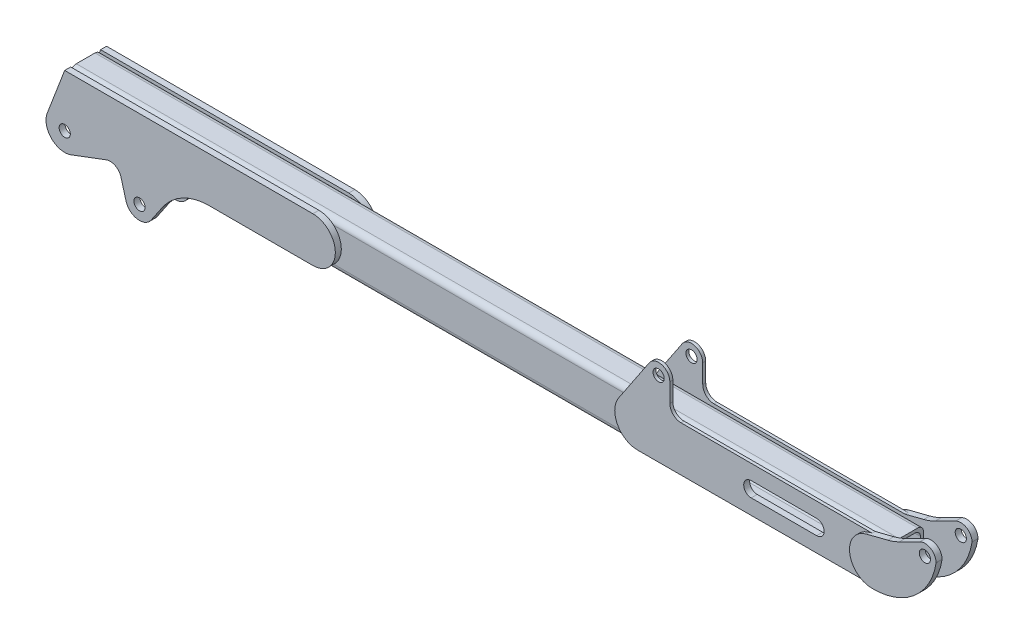
SolidWorks part; units mm, degrees
ref_plane "Front Plane" through (0, 0, 0) normal (0, 0, 1) x (1, 0, 0)
ref_plane "Top Plane" through (0, 0, 0) normal (0, 1, 0) x (1, 0, 0)
ref_plane "Right Plane" through (0, 0, 0) normal (1, 0, 0) x (0, 0, -1)
sketch "Sketch2" plane through (0, 0, 0) normal (1, 0, 0) x (0, 0, -1)
  line L0 (0, 0) -> (0, 180.6275) construction
  line L1 (-32, 132) -> (32, 132)
  line L2 (-40, 140) -> (40, 140)
  line L3 (-40, 140) -> (-40, 20)
  line L4 (-40, 20) -> (40, 20)
  line L5 (40, 140) -> (40, 20)
  line L6 (-40, 140) -> (40, 20) construction
  line L7 (-40, 20) -> (40, 140) construction
  line L8 (32, 132) -> (32, 28)
  line L9 (-32, 28) -> (32, 28)
  line L10 (-32, 132) -> (-32, 28)
  point P2 (0, 80)
  dimension "D1" = 80
  dimension "D2" = 120
  dimension "D4" = 80
  dimension "D3" = 8
extrude "Boss-Extrude1" add sketch "Sketch2" along normal blind 2200
fillet "Fillet4" radius 15 8 edges at (1100, 20, -40) (1100, 28, 32) (1100, 132, 32) (1100, 132, -32) (1100, 28, -32) (1100, 20, 40) (1100, 140, -40) (1100, 140, 40)
sketch "Sketch3" plane through (0, 0, 40) normal (0, 0, 1) x (1, 0, 0)
  line L0 (0, 80) -> (2300, 80) construction
  line L1 (0, 125) -> (0, 35) construction
  line L2 (-1929.687, -1730.7826) -> (-1056.3536, -1730.7826) construction
  line L3 (148.6635, -712.4908) -> (749.3302, -712.4908) construction
  line L4 (0, 0) -> (0, -650) construction
  line L5 (0, -650) -> (100, -650) construction
  dimension "D1" = 100
  dimension "D2" = 650
  dimension "D5" = 2300
sketch "Sketch4" plane through (0, 0, 40) normal (0, 0, 1) x (1, 0, 0)
  line L0 (0, 0) -> (200, 0.9743) construction
  line L1 (0, 80) -> (2300, 80) construction
  line L2 (663.6168, 140) -> (0, 140)
  line L3 (0, 140) -> (-46.7025, 17.8571)
  line L4 (17.6358, -46.7865) -> (141.757, 0)
  line L5 (141.757, 0) -> (163.854, -79.9858)
  line L6 (231.0313, -91.055) -> (306.383, 20)
  line L7 (2200, 20) -> (0, 20) construction
  line L8 (306.383, 20) -> (663.6168, 20)
  line L9 (200, 0.9743) -> (200, -70) construction
  circle A0 centre (0, 0) radius 15
  circle A1 centre (200, -70) radius 15
  arc A2 (663.6168, 20) -> (663.6168, 140) centre (663.6168, 80) ccw
  arc A3 (163.854, -79.9858) -> (231.0313, -91.055) centre (200, -70) ccw
  arc A4 (-46.7025, 17.8571) -> (17.6358, -46.7865) centre (0, 0) ccw
  dimension "D1" = 30
  dimension "D2" = 30
  dimension "D5" = 120
  dimension "D6" = 75
  dimension "D7" = 100
  dimension "D3" = 200
  dimension "D4" = 150
extrude "Boss-Extrude2" add sketch "Sketch4" along normal blind 16
fillet "Fillet1" radius 30 1 edges at (141.757, 0, 48)
fillet "Fillet2" radius 150 1 edges at (306.383, 20, 48)
ref_plane "Plane1" through (0, 0, 0) normal (0, 0, -1) x (-1, 0, 0)
mirror "Mirror1" about plane through (0, 0, 0) normal (0, 0, -1) of "Fillet2", "Fillet1", "Boss-Extrude2"
sketch "Sketch5" plane through (0, 0, 40) normal (0, 0, 1) x (1, 0, 0)
  line L1 (2300, 165) -> (2300, 80) construction
  line L2 (2286.519, 191.8004) -> (2216.8615, 156.7617)
  line L3 (2216.8615, 156.7617) -> (2143.6382, 138.1512)
  line L4 (0, 80) -> (2300, 80) construction
  circle A0 centre (2158.418, 80) radius 60
  circle A1 centre (2300, 165) radius 15
  circle A2 centre (2300, 165) radius 30
  arc A3 (2156.4729, 20.0315) -> (2330, 165) centre (2161.9788, 189.7811) ccw
  dimension "D1" = 30
  dimension "D2" = 60
  dimension "D3" = 85
  dimension "D4" = 120
extrude "Boss-Extrude3" add sketch "Sketch5" along normal blind 16 separate body
fillet "Fillet3" radius 150 1 edges at (2216.8615, 156.7617, 48)
sketch "Sketch9" plane through (0, 0, 40) normal (0, 0, 1) x (1, 0, 0)
  line L0 (0, 80) -> (2300, 80) construction
  line L1 (1610, 140) -> (2157.5508, 140)
  line L2 (0, 140) -> (2200, 140) construction
  line L3 (2157.5508, 140) -> (2157.5508, 20)
  line L4 (2157.5508, 20) -> (1524.007, 18.707)
  line L5 (2200, 20) -> (0, 20) construction
  line L6 (1473.0598, 114.0766) -> (1555.0638, 236.6789)
  line L7 (1610, 220) -> (1610, 140)
  arc A0 (1473.0598, 114.0766) -> (1524.007, 18.707) centre (1524.007, 80) ccw
  arc A1 (2156.4729, 20.0315) -> (2330, 165) centre (2161.9788, 189.7811) ccw construction
  circle A2 centre (1580, 220) radius 15
  arc A3 (1610, 220) -> (1555.0638, 236.6789) centre (1580, 220) ccw
  dimension "D1" = 30
  dimension "D2" = 60
  dimension "D3" = 1580
  dimension "D4" = 220
extrude "Boss-Extrude4" add sketch "Sketch9" along normal blind 8
fillet "Fillet5" radius 30 1 edges at (1610, 140, 44)
mirror "Mirror5" about plane through (0, 0, 0) normal (0, 0, -1) of "Fillet3", "Boss-Extrude3", "Fillet5", "Boss-Extrude4"
sketch "Sketch6" plane through (0, 0, 40) normal (0, 0, 1) x (1, 0, 0)
  line L0 (1827.553, 80) -> (2002.553, 80) construction
  line L1 (0, 80) -> (2300, 80) construction
  line L2 (1827.553, 100) -> (2002.553, 100)
  line L3 (1827.553, 60) -> (2002.553, 60)
  arc A0 (1827.553, 100) -> (1827.553, 60) centre (1827.553, 80) ccw
  arc A1 (2002.553, 60) -> (2002.553, 100) centre (2002.553, 80) ccw
  point P4 (1915.053, 80)
  dimension "D2" = 20
  dimension "D1" = 175
extrude "Cut-Extrude1" cut sketch "Sketch6" against normal through all both and the other way through all
